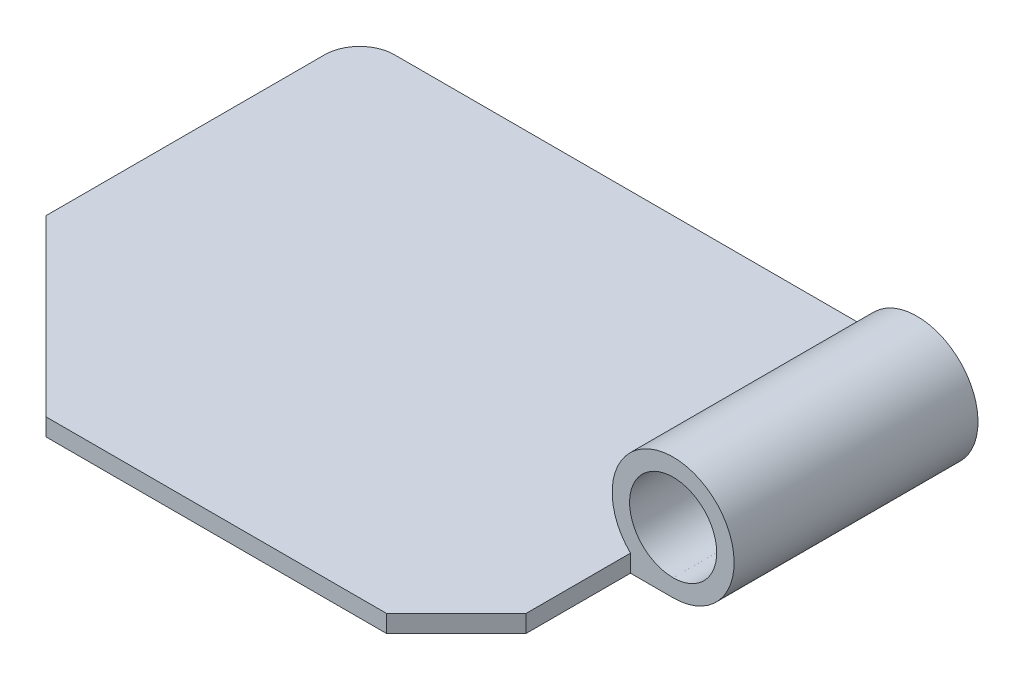
SolidWorks part; units mm, degrees
ref_plane "Front Plane" through (0, 0, 0) normal (0, 0, 1) x (1, 0, 0)
ref_plane "Top Plane" through (0, 0, 0) normal (0, 1, 0) x (1, 0, 0)
ref_plane "Right Plane" through (0, 0, 0) normal (1, 0, 0) x (0, 0, -1)
sketch "Sketch1" plane through (0, 0, 0) normal (0, 1, 0) x (1, 0, 0)
  line L0 (0, 0) -> (97.75, 0)
  line L1 (97.75, 0) -> (117.747, 19.997)
  line L2 (117.747, 19.997) -> (117.747, 49.997)
  line L3 (117.747, 49.997) -> (130.0005, 49.997)
  line L4 (130.0005, 49.997) -> (130.0005, 119.997)
  line L6 (117.7505, 119.997) -> (117.7505, 139.9995)
  line L7 (117.7505, 139.9995) -> (-39.9995, 139.9995)
  line L8 (-49.9995, 129.9995) -> (-49.9995, 49.9995)
  line L9 (-49.9995, 49.9995) -> (0, 0)
  line L10 (117.7505, 119.997) -> (130.0005, 119.997)
  arc A0 (-49.9995, 129.9995) -> (-39.9995, 139.9995) centre (-39.9995, 129.9995) cw
  dimension "D2" = 10
  dimension "D1" = 97.75
  dimension "D3" = 157.75
  dimension "D4" = 135
  dimension "D5" = 135
  dimension "D6" = 80
  dimension "D7" = 12.25
  dimension "D8" = 30
  dimension "D9" = 70
  dimension "D10" = 70.71
  dimension "D11" = 28.28
extrude "Boss-Extrude1" add sketch "Sketch1" against normal blind 5
ref_plane "Plane2" through (0, 0, -119.997) normal (0, 0, -1) x (-1, 0, 0)
sketch "Sketch2" plane through (0, 0, -119.997) normal (0, 0, -1) x (-1, 0, 0)
  line L0 (-130.0005, -30.512) -> (-130.0005, 30) construction
  circle A0 centre (-129.9875, 12.5) radius 17.5
  circle A1 centre (-129.9875, 12.5) radius 12.5
  dimension "D1" = 35
  dimension "D2" = 25
extrude "Boss-Extrude2" add sketch "Sketch2" against normal blind 70
